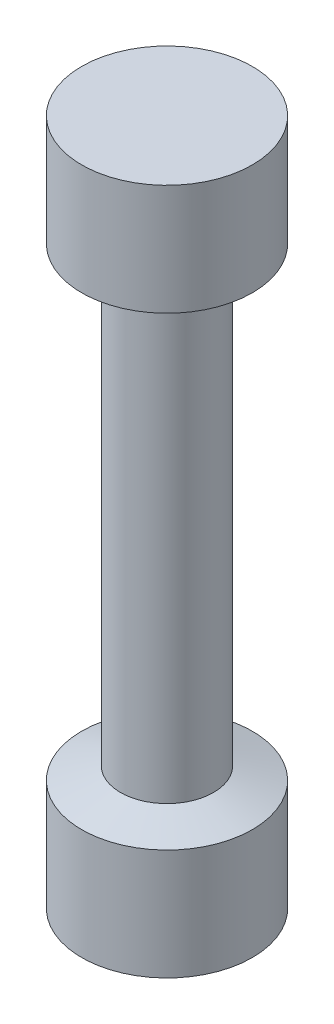
SolidWorks part; units mm, degrees
ref_plane "Plano frontal" through (0, 0, 0) normal (0, 0, 1) x (1, 0, 0)
ref_plane "Plano superior" through (0, 0, 0) normal (0, 1, 0) x (1, 0, 0)
ref_plane "Plano direito" through (0, 0, 0) normal (1, 0, 0) x (0, 0, -1)
sketch "Esboço2" plane through (0, 0, 0) normal (0, 0, 1) x (1, 0, 0)
  line L0 (0, -28.7093) -> (0, 1406.7566) construction
  line L1 (-6.7, 8.7) -> (-3.65, 9.7)
  line L2 (0, 0) -> (-6.7, 0)
  line L3 (0, 0) -> (0, 8.7)
  line L4 (0, 8.7) -> (-6.7, 8.7)
  line L5 (-6.7, 0) -> (-6.7, 8.7)
  line L6 (0, 8.7) -> (-3.65, 8.7)
  line L7 (0, 8.7) -> (0, 45.2)
  line L8 (0, 26.95) -> (-3.65, 26.95)
  line L9 (-3.65, 8.7) -> (-3.65, 45.2)
  line L10 (-1000, 26.95) -> (49000, 26.95) construction
  line L11 (-6.7, 45.2) -> (-3.65, 44.2)
  line L12 (0, 45.2) -> (-6.7, 45.2)
  line L13 (-6.7, 53.9) -> (-6.7, 45.2)
  line L14 (0, 53.9) -> (-6.7, 53.9)
  line L15 (0, 53.9) -> (0, 45.2)
  line L16 (0, 45.2) -> (-3.65, 45.2)
  dimension "D1" = 6.7
  dimension "D2" = 8.7
  dimension "D3" = 1
  dimension "D5" = 18.25
  dimension "D6" = 3.65
revolve "Revolução1" add sketch "Esboço2" angle 360 about L0
